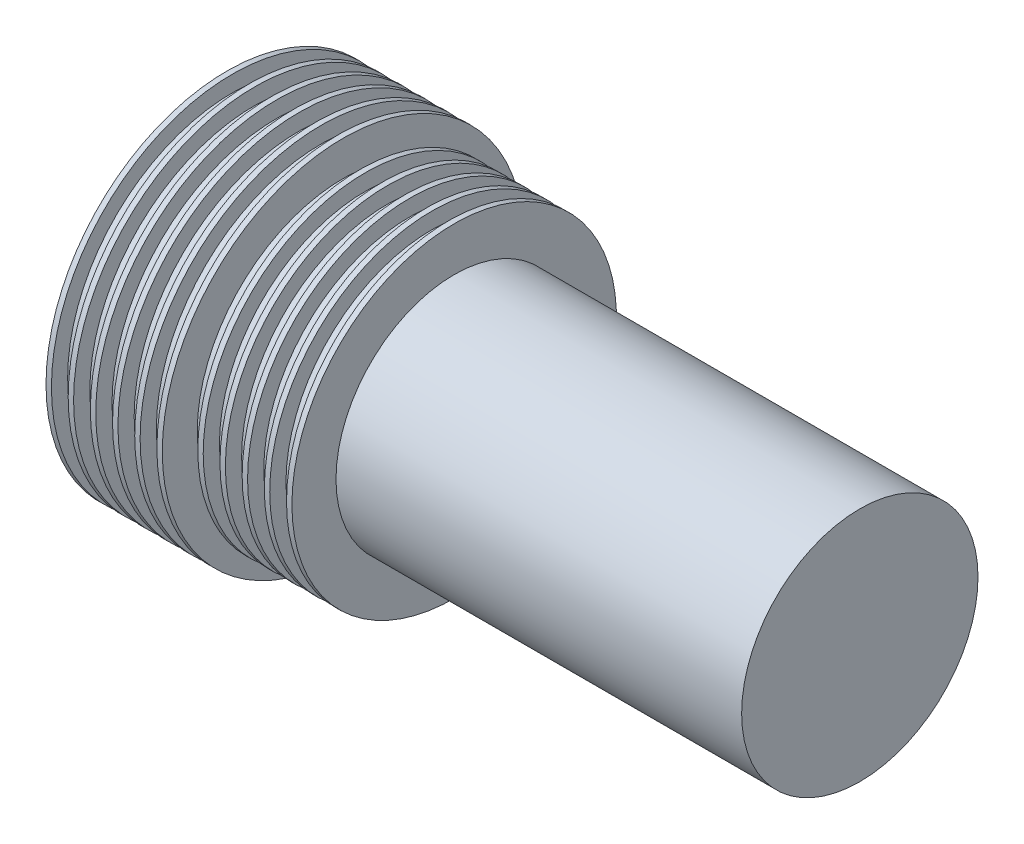
SolidWorks part; units mm, degrees
ref_plane "Front Plane" through (0, 0, 0) normal (0, 0, 1) x (1, 0, 0)
ref_plane "Top Plane" through (0, 0, 0) normal (0, 1, 0) x (1, 0, 0)
ref_plane "Right Plane" through (0, 0, 0) normal (1, 0, 0) x (0, 0, -1)
sketch "Sketch1" plane through (0, 0, 0) normal (0, 0, 1) x (1, 0, 0)
  line L0 (0, 0) -> (29.718, 0)
  line L1 (29.718, 0) -> (29.718, 5.5499)
  line L2 (29.718, 5.5499) -> (17.018, 5.5499)
  line L3 (5.461, 7.62) -> (5.461, 8.5)
  line L5 (0, 8.5) -> (0, 0)
  line L8 (0, 8.5) -> (0.254, 8.5)
  line L9 (0.254, 8.5) -> (0.254, 7.738)
  line L10 (0.254, 7.738) -> (1.0414, 7.738)
  line L11 (1.0414, 7.738) -> (1.0414, 8.5)
  line L12 (1.0414, 8.5) -> (1.2954, 8.5)
  line L13 (1.2954, 8.5) -> (1.2954, 7.738)
  line L14 (1.2954, 7.738) -> (2.0828, 7.738)
  line L15 (2.0828, 7.738) -> (2.0828, 8.5)
  line L16 (2.0828, 8.5) -> (2.3368, 8.5)
  line L17 (2.3368, 8.5) -> (2.3368, 7.738)
  line L18 (2.3368, 7.738) -> (3.1242, 7.738)
  line L19 (3.1242, 7.738) -> (3.1242, 8.5)
  line L20 (3.1242, 8.5) -> (3.3782, 8.5)
  line L21 (3.3782, 8.5) -> (3.3782, 7.738)
  line L22 (3.3782, 7.738) -> (4.1656, 7.738)
  line L23 (4.1656, 7.738) -> (4.1656, 8.5)
  line L24 (4.1656, 8.5) -> (4.4196, 8.5)
  line L25 (4.4196, 8.5) -> (4.4196, 7.738)
  line L26 (4.4196, 7.738) -> (5.207, 7.738)
  line L27 (5.207, 7.738) -> (5.207, 8.5)
  line L28 (5.207, 8.5) -> (5.461, 8.5)
  line L31 (10.668, 5.5499) -> (17.018, 5.5499)
  line L33 (5.461, 7.62) -> (5.461, 6.858)
  line L34 (5.461, 6.858) -> (6.2484, 6.858)
  line L35 (6.2484, 6.858) -> (6.2484, 7.62)
  line L36 (6.2484, 7.62) -> (6.5024, 7.62)
  line L37 (6.5024, 7.62) -> (6.5024, 6.858)
  line L38 (6.5024, 6.858) -> (7.2898, 6.858)
  line L39 (7.2898, 6.858) -> (7.2898, 7.62)
  line L40 (7.2898, 7.62) -> (7.5438, 7.62)
  line L41 (7.5438, 7.62) -> (7.5438, 6.858)
  line L42 (7.5438, 6.858) -> (8.3312, 6.858)
  line L43 (8.3312, 6.858) -> (8.3312, 7.62)
  line L44 (8.3312, 7.62) -> (8.5852, 7.62)
  line L45 (8.5852, 7.62) -> (8.5852, 6.858)
  line L46 (8.5852, 6.858) -> (9.3726, 6.858)
  line L47 (9.3726, 6.858) -> (9.3726, 7.62)
  line L48 (9.3726, 7.62) -> (9.6266, 7.62)
  line L49 (9.6266, 7.62) -> (9.6266, 6.858)
  line L50 (9.6266, 6.858) -> (10.414, 6.858)
  line L51 (10.414, 6.858) -> (10.414, 7.62)
  line L52 (10.414, 7.62) -> (10.668, 7.62)
  line L53 (10.668, 7.62) -> (10.668, 5.5499)
  point P29 (0, 0)
  dimension "D2" = 5.5499
  dimension "D4" = 5.461
  dimension "D3" = 8.5
  dimension "D7" = 0.7874
  dimension "D8" = 0.254
  dimension "D9" = 0.762
  dimension "D1" = 7.62
  dimension "D5" = 19.05
revolve "Revolve1" add sketch "Sketch1" angle 360 about L0
cosmetic thread "Cosmetic Thread1" parameters "D2"=9.6012
equation "\"after_laby_len\"=0.75in"
equation "\"Cavity_Depth\" = 0.031in"
equation "\"Cavity_Width\" = 0.031in"
equation "\"Tooth_Width\" = .01in"
equation "\"Shaft_Seal_OD\"= 17mm'diameter at seal area"
equation "\"Shaft_clearance\"= .002in"
equation "\"O-Ring_ID\"= .801in"
equation "\"O-Ring_CS\"= .070in"
equation "\"Shaft_OD\"= .5in"
equation "\"D3@Sketch1\"=\"Shaft_Seal_OD\"/2"
equation "\"D7@Sketch1\"=\"Cavity_Width\""
equation "\"D8@Sketch1\"=\"Tooth_Width\""
equation "\"D4@Sketch1\"=6*\"Tooth_Width\"+5*\"Cavity_Width\""
equation "\"seal2dia\"=0.3in"
equation "\"D1@Sketch1\"=\"seal2dia\""
equation "\"D5@Sketch1\"=\"after_laby_len\""
equation "\"Flange_OD\"=2.3in"
